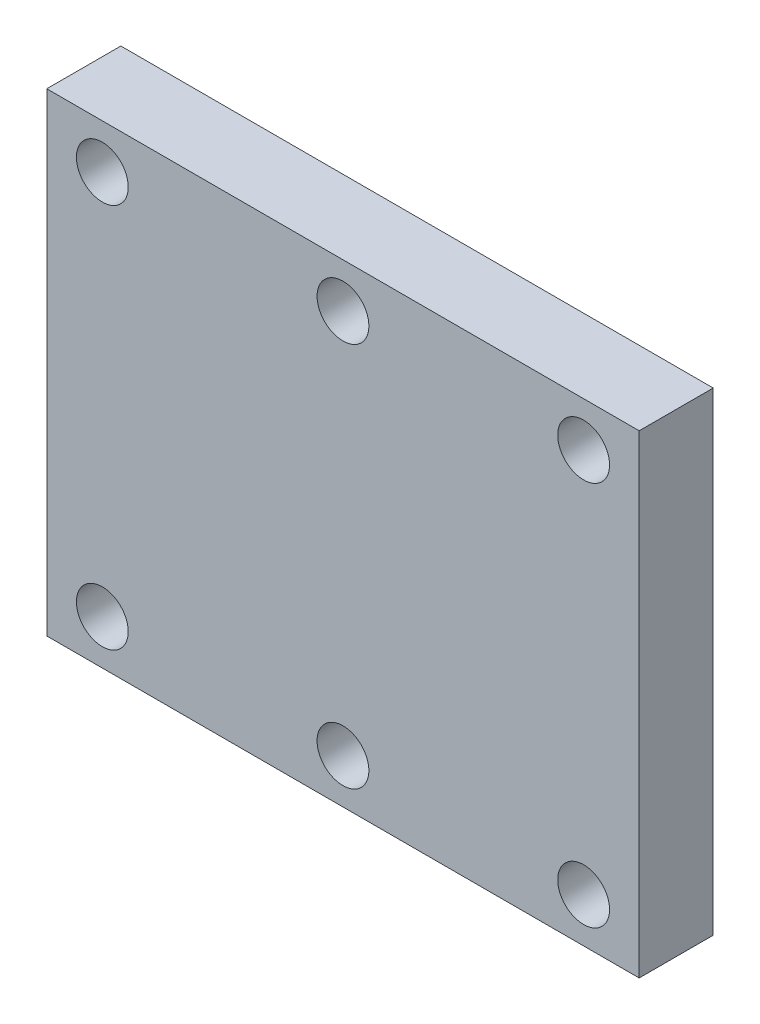
SolidWorks part; units mm, degrees
ref_plane "Front Plane" through (0, 0, 0) normal (0, 0, 1) x (1, 0, 0)
ref_plane "Top Plane" through (0, 0, 0) normal (0, 1, 0) x (1, 0, 0)
ref_plane "Right Plane" through (0, 0, 0) normal (1, 0, 0) x (0, 0, -1)
sketch "Sketch1" plane through (0, 0, 0) normal (0, 0, 1) x (1, 0, 0)
  line L0 (-79.4339, 0) -> (75.3991, 0) construction
  line L1 (0, 32) -> (80, 32)
  line L2 (0, 32) -> (0, -32)
  line L3 (0, -32) -> (80, -32)
  line L4 (80, 32) -> (80, -32)
  dimension "D1" = 64
  dimension "D2" = 80
extrude "Boss-Extrude1" add sketch "Sketch1" along normal blind 10
sketch "Sketch2" plane through (0, 0, 10) normal (0, 0, 1) x (1, 0, 0)
  line L1 (0, 32) -> (0, -32) construction
  point P0 (7.5, -26)
  dimension "D1" = 26
  dimension "D2" = 7.5
hole_wizard "Ø7.0 (7) Diameter Hole1" positions "Sketch3" profile "Sketch4" hole size "Ø7.0" standard "ISO"
sketch "Sketch3" plane through (0, 0, 10) normal (0, 0, 1) x (1, 0, 0)
  point P0 (7.5, -26)
sketch "Sketch4" plane through (7.5, -26, 10) normal (1, 0, 0) x (0, -1, 0)
  line L0 (0, 0) -> (0, 28.103)
  line L1 (0, 28.103) -> (3.5, 26)
  line L2 (3.5, 26) -> (3.5, 0)
  line L5 (3.5, 0) -> (0, 0)
  line L10 (0, 28.103) -> (-3.5, 26) construction
  line L11 (0, -6.35) -> (0, 107.95) construction
  dimension "Hole Dia." = 7
  dimension "Hole Depth" = 26
  dimension "Drill Angle" = 118
pattern_linear "LPattern1" count 3 spacing 32.5 along (1, 0, 0) count 2 spacing 52 along (0, 1, 0) of "Ø7.0 (7) Diameter Hole1"
